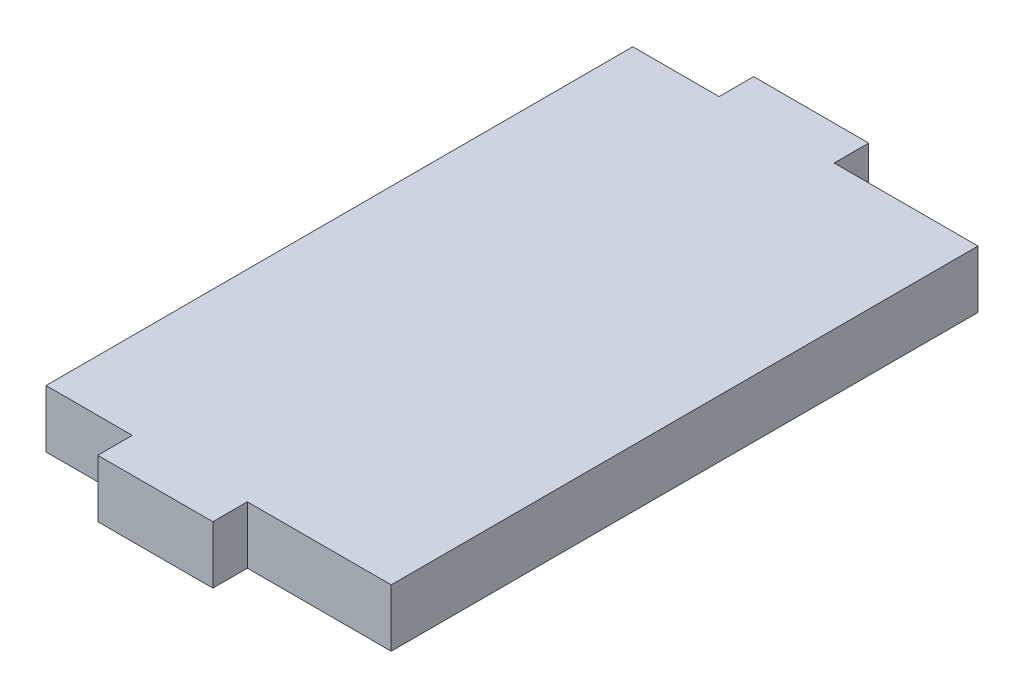
SolidWorks part; units mm, degrees
material "Acier S235"
ref_plane "Plan de face" through (0, 0, 0) normal (0, 0, 1) x (1, 0, 0)
ref_plane "Plan de dessus" through (0, 0, 0) normal (0, 1, 0) x (1, 0, 0)
ref_plane "Plan de droite" through (0, 0, 0) normal (1, 0, 0) x (0, 0, -1)
sketch "Esquisse1" plane through (0, 0, 0) normal (0, 1, 0) x (1, 0, 0)
  line L0 (15, 25.5) -> (2.5, 25.5)
  line L1 (-15, -28.5) -> (15, -28.5) construction
  line L2 (-15, -28.5) -> (-15, 28.5) construction
  line L3 (-15, 28.5) -> (15, 28.5) construction
  line L4 (15, -28.5) -> (15, 28.5) construction
  line L5 (-15, -28.5) -> (15, 28.5) construction
  line L6 (-15, 28.5) -> (15, -28.5) construction
  line L7 (2.5, 25.5) -> (2.5, 28.5)
  line L8 (2.5, 28.5) -> (-7.5, 28.5)
  line L9 (-7.5, 28.5) -> (-7.5, 25.5)
  line L10 (-7.5, 25.5) -> (-15, 25.5)
  line L11 (-15, 25.5) -> (-15, -25.5)
  line L12 (-15, -25.5) -> (-7.5, -25.5)
  line L13 (-7.5, -25.5) -> (-7.5, -28.5)
  line L14 (-7.5, -28.5) -> (2.5, -28.5)
  line L15 (2.5, -28.5) -> (2.5, -25.5)
  line L16 (2.5, -25.5) -> (15, -25.5)
  line L17 (15, -25.5) -> (15, 25.5)
  point P0 (0, 0)
  point P8 (-12.5, 31.9584)
  point P19 (-12.5, 28.5)
  point P20 (-12.5, 24.7874)
  point P21 (-12.5, 11.2327)
  point P22 (-10, 25.8301)
  point P23 (-12.5, -25.5)
  point P24 (0, 0)
  point P25 (-12.5, -28.5)
  point P26 (-12.5, -28.5)
  point P27 (0, 0)
  point P28 (-12.5, 25.5)
  point P29 (-12.5, 25.5)
  point P30 (-12.5, -25.5)
  point P31 (-12.5, -28.5)
  dimension "D1" = 51
  dimension "D2" = 12.5
  dimension "D3" = 10
  dimension "D4" = 57
  dimension "D5" = 3
  dimension "D6" = 7.5
extrude "Boss.-Extru.1" add sketch "Esquisse1" along normal blind 5
